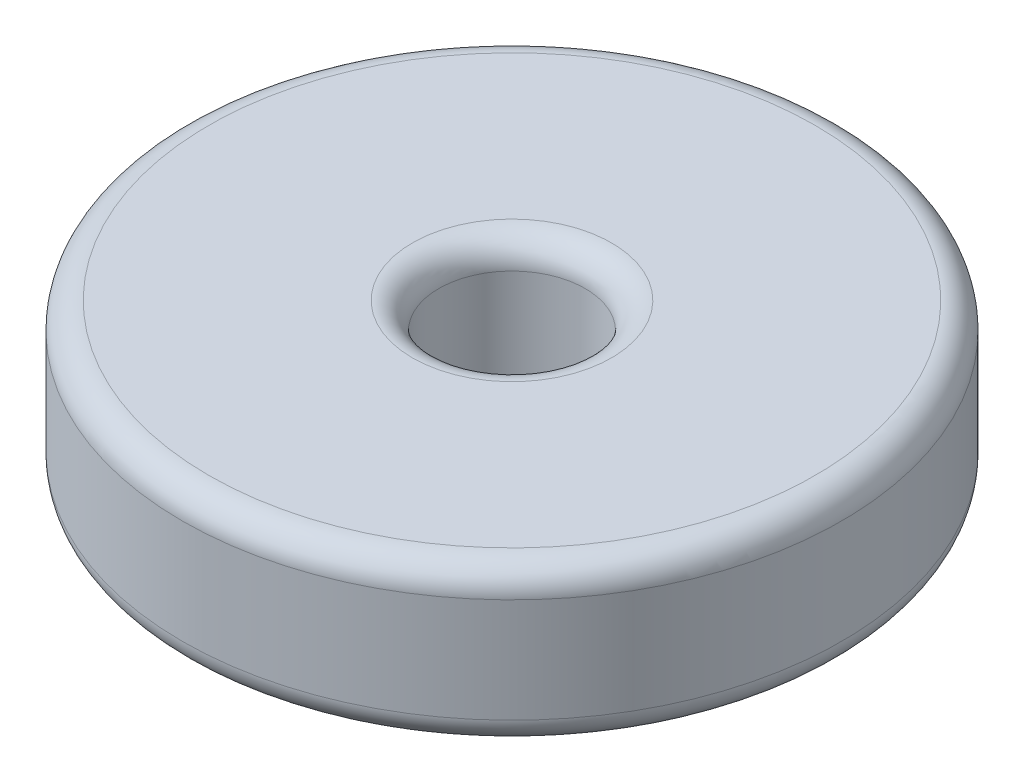
SolidWorks part; units mm, degrees
ref_plane "Front Plane" through (0, 0, 0) normal (0, 0, 1) x (1, 0, 0)
ref_plane "Top Plane" through (0, 0, 0) normal (0, 1, 0) x (1, 0, 0)
ref_plane "Right Plane" through (0, 0, 0) normal (1, 0, 0) x (0, 0, -1)
sketch "Sketch1" plane through (0, 0, 0) normal (0, 1, 0) x (1, 0, 0)
  circle A0 centre (0, 0) radius 12.5
extrude "Boss-Extrude1" add sketch "Sketch1" along normal blind 5.9531
sketch "Sketch2" plane through (0, 5.9531, 0) normal (0, 1, 0) x (1, 0, 0)
  circle A0 centre (0, 0) radius 2.7781
extrude "Cut-Extrude1" cut sketch "Sketch2" against normal up to surface (5.9531 mm away) up to face at (0, 0, 12.5)
fillet "Fillet1" radius 1 4 edges at (0, 0, 2.7781) (0, 0, 12.5) (0, 5.9531, 12.5) (0, 5.9531, 2.7781)
